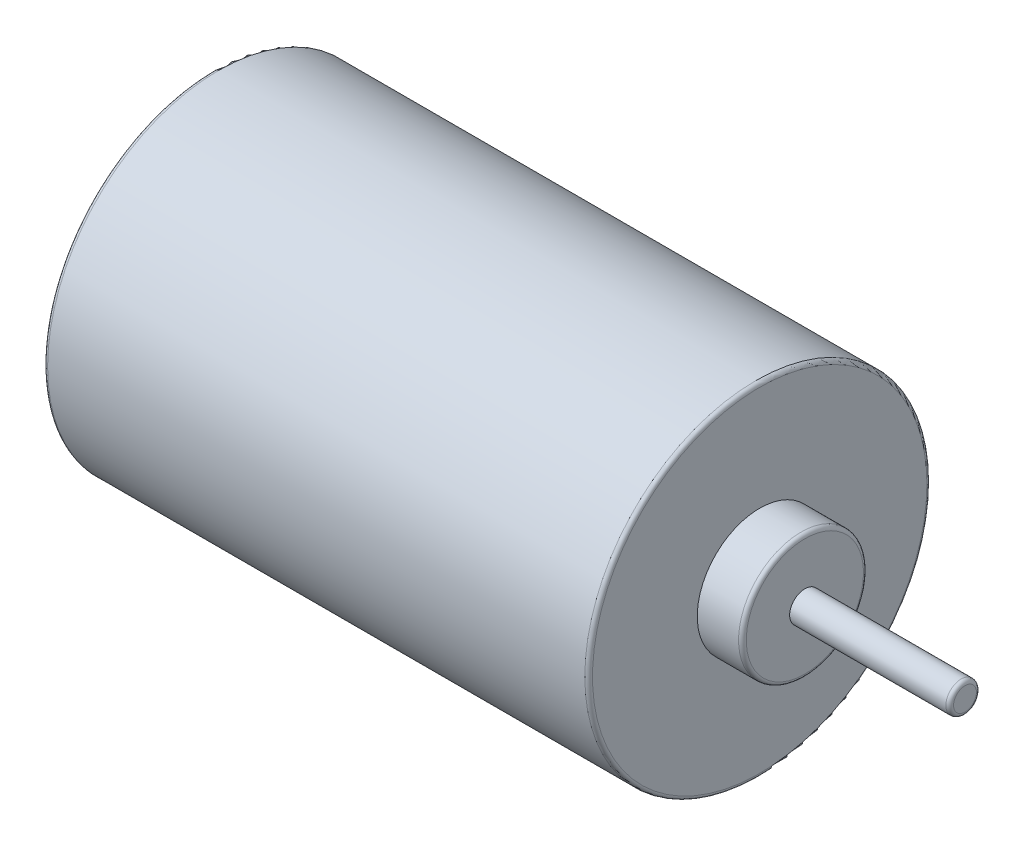
SolidWorks part; units mm, degrees
ref_plane "Alzado" through (0, 0, 0) normal (0, 0, 1) x (1, 0, 0)
ref_plane "Planta" through (0, 0, 0) normal (0, 1, 0) x (1, 0, 0)
ref_plane "Vista lateral" through (0, 0, 0) normal (1, 0, 0) x (0, 0, -1)
sketch "Croquis1" plane through (0, 0, 0) normal (1, 0, 0) x (0, 0, -1)
  circle A0 centre (0, 0) radius 17.8
  dimension "D1" = 35.6
extrude "Saliente-Extruir1" add sketch "Croquis1" along normal blind 56.7
sketch "Croquis2" plane through (0, 0, 0) normal (-1, 0, 0) x (0, 0, 1)
  circle A0 centre (0, 0) radius 6
  dimension "D1" = 12
extrude "Saliente-Extruir2" add sketch "Croquis2" along normal blind 1
sketch "Croquis3" plane through (-1, 0, 0) normal (-1, 0, 0) x (0, 0, 1)
  circle A0 centre (0, 0) radius 5
extrude "Saliente-Extruir3" add sketch "Croquis3" along normal blind 1
sketch "Croquis4" plane through (56.7, 0, 0) normal (1, 0, 0) x (0, 0, -1)
  circle A0 centre (0, 0) radius 6.5
  dimension "D1" = 13
extrude "Saliente-Extruir4" add sketch "Croquis4" along normal blind 4.7
sketch "Croquis5" plane through (61.4, 0, 0) normal (1, 0, 0) x (0, 0, -1)
  circle A0 centre (0, 0) radius 1.5875
  dimension "D1" = 3.175
extrude "Saliente-Extruir5" add sketch "Croquis5" along normal blind 16.66
fillet "Redondeo1" radius 0.4 6 edges at (78.06, 0, -1.5875) (61.4, 0, -6.5) (56.7, 0, -17.8) (0, 0, -17.8) (-1, 0, 6) (-2, 0, 5)
